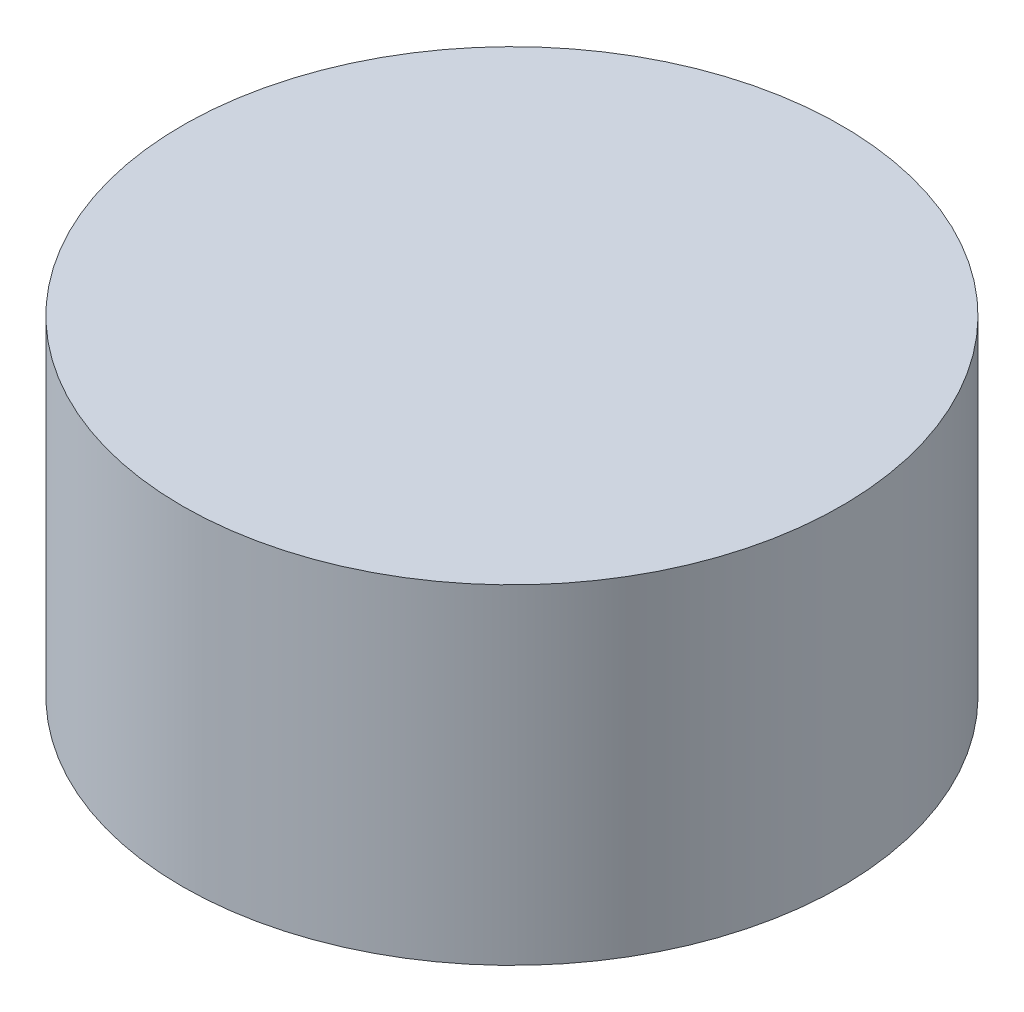
SolidWorks part; units mm, degrees
ref_plane "Front Plane" through (0, 0, 0) normal (0, 0, 1) x (1, 0, 0)
ref_plane "Top Plane" through (0, 0, 0) normal (0, 1, 0) x (1, 0, 0)
ref_plane "Right Plane" through (0, 0, 0) normal (1, 0, 0) x (0, 0, -1)
sketch "Sketch1" plane through (0, 0, 0) normal (0, 1, 0) x (1, 0, 0)
  circle A0 centre (0, 0) radius 0.7938
  dimension "D1" = 1.5875
extrude "Boss-Extrude1" add sketch "Sketch1" along normal blind 0.7937
